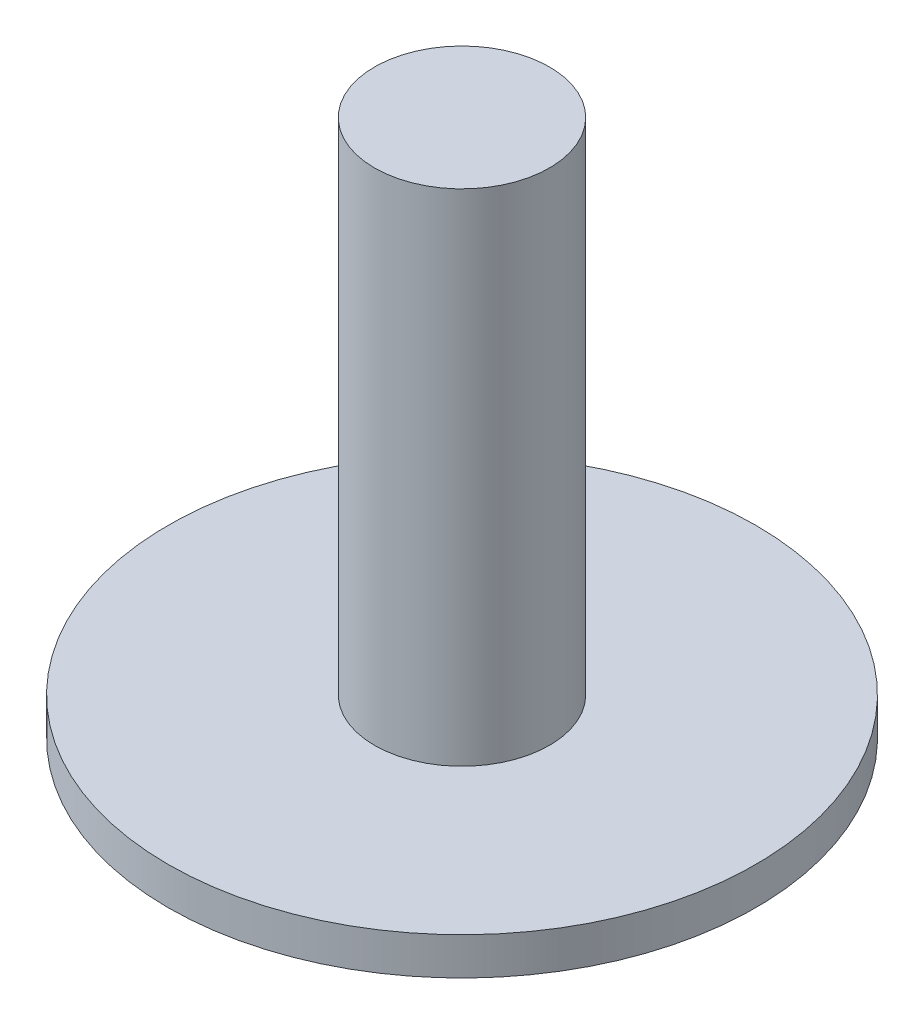
SolidWorks part; units mm, degrees
ref_plane "Front Plane" through (0, 0, 0) normal (0, 0, 1) x (1, 0, 0)
ref_plane "Top Plane" through (0, 0, 0) normal (0, 1, 0) x (1, 0, 0)
ref_plane "Right Plane" through (0, 0, 0) normal (1, 0, 0) x (0, 0, -1)
sketch "Sketch1" plane through (0, 0, 0) normal (0, 1, 0) x (1, 0, 0)
  circle A0 centre (0, 0) radius 11.75
  dimension "D1" = 23.5
extrude "Boss-Extrude1" add sketch "Sketch1" along normal blind 1.5
sketch "Sketch2" plane through (0, 1.5, 0) normal (0, 1, 0) x (1, 0, 0)
  circle A0 centre (0, 0) radius 3.5
  dimension "D1" = 7
extrude "Boss-Extrude2" add sketch "Sketch2" along normal blind 20
